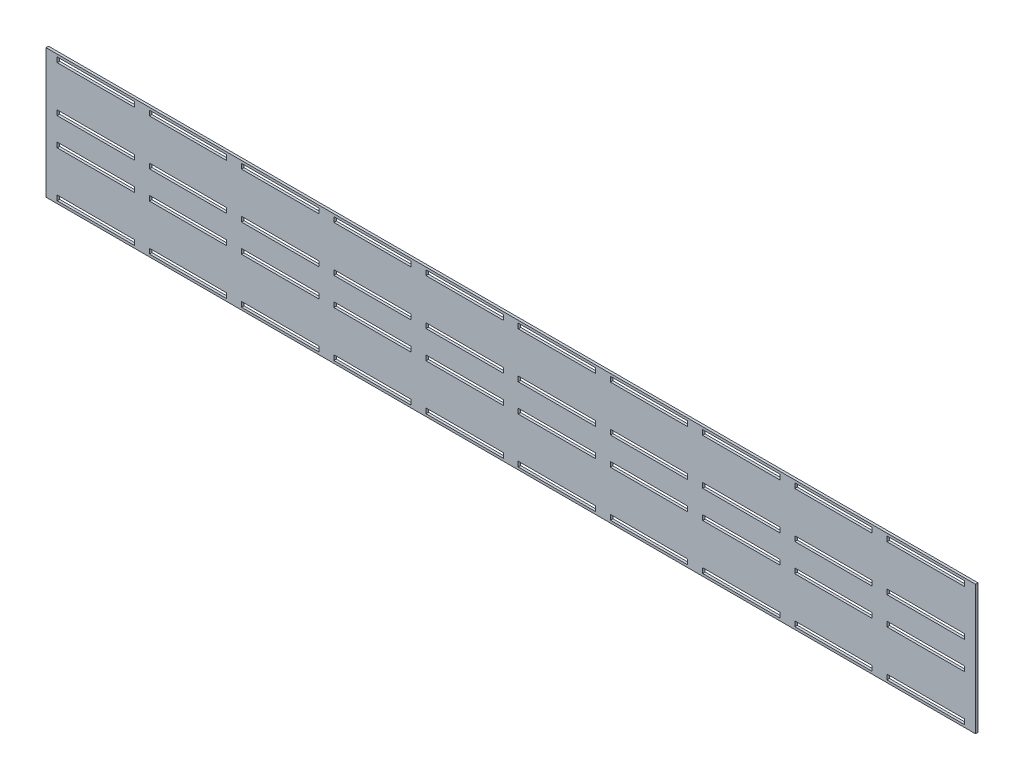
SolidWorks part; units mm, degrees
material "ABS"
ref_plane "Płaszczyzna przednia" through (0, 0, 0) normal (0, 0, 1) x (1, 0, 0)
ref_plane "Płaszczyzna górna" through (0, 0, 0) normal (0, 1, 0) x (1, 0, 0)
ref_plane "Płaszczyzna prawa" through (0, 0, 0) normal (1, 0, 0) x (0, 0, -1)
sketch "Szkic1" plane through (0, 0, 0) normal (0, 0, 1) x (1, 0, 0)
  line L1 (-187, 26.5) -> (187, 26.5)
  line L2 (-187, 26.5) -> (-187, -26.5)
  line L3 (-187, -26.5) -> (187, -26.5)
  line L4 (187, 26.5) -> (187, -26.5)
  line L5 (-187, 26.5) -> (187, -26.5) construction
  line L6 (-187, -26.5) -> (187, 26.5) construction
  point P0 (0, 0)
  dimension "D1" = 374
  dimension "D2" = 53
extrude "Dodanie-wyciągnięcie1" add sketch "Szkic1" along normal blind 1
sketch "Szkic6" plane through (0, 0, 0) normal (0, 0, -1) x (-1, 0, 0)
  line L2 (-182, -6.6) -> (-151, -6.6)
  line L8 (-145, -6.6) -> (-114, -6.6)
  line L13 (-108, -6.6) -> (-77, -6.6)
  line L15 (-182, -6.6) -> (-182, -4.6)
  line L20 (-182, -4.6) -> (-151, -4.6)
  line L23 (-34, -6.6) -> (-3, -6.6)
  line L25 (-151, -4.6) -> (-151, -6.6)
  line L28 (3, -6.6) -> (34, -6.6)
  line L33 (40, -6.6) -> (71, -6.6)
  line L38 (77, -6.6) -> (108, -6.6)
  line L43 (114, -6.6) -> (145, -6.6)
  line L45 (-145, -6.6) -> (-145, -4.6)
  line L48 (151, -6.6) -> (182, -6.6)
  line L50 (-145, -4.6) -> (-114, -4.6)
  line L51 (-114, -4.6) -> (-114, -6.6)
  line L55 (-108, -6.6) -> (-108, -4.6)
  line L56 (-108, -4.6) -> (-77, -4.6)
  line L57 (-77, -4.6) -> (-77, -6.6)
  line L67 (-34, -6.6) -> (-34, -4.6)
  line L68 (-34, -4.6) -> (-3, -4.6)
  line L69 (-3, -4.6) -> (-3, -6.6)
  line L73 (3, -6.6) -> (3, -4.6)
  line L74 (3, -4.6) -> (34, -4.6)
  line L75 (34, -4.6) -> (34, -6.6)
  line L79 (40, -6.6) -> (40, -4.6)
  line L80 (40, -4.6) -> (71, -4.6)
  line L81 (71, -4.6) -> (71, -6.6)
  line L82 (77, -6.6) -> (77, -4.6)
  line L83 (77, -4.6) -> (108, -4.6)
  line L84 (108, -4.6) -> (108, -6.6)
  line L91 (114, -6.6) -> (114, -4.6)
  line L92 (114, -4.6) -> (145, -4.6)
  line L93 (145, -4.6) -> (145, -6.6)
  line L94 (151, -6.6) -> (151, -4.6)
  line L95 (151, -4.6) -> (182, -4.6)
  line L96 (182, -4.6) -> (182, -6.6)
  line L100 (-114, -25) -> (-114, -23)
  line L101 (-187, 26.5) -> (187, 26.5) construction
  line L102 (-187, -26.5) -> (-187, 26.5) construction
  line L103 (-182, 25) -> (-151, 25)
  line L104 (-182, 25) -> (-182, 23)
  line L105 (-182, 23) -> (-151, 23)
  line L106 (-151, 25) -> (-151, 23)
  line L107 (-151, -25) -> (-151, -23)
  line L108 (-182, -23) -> (-151, -23)
  line L109 (-182, -25) -> (-182, -23)
  line L110 (-182, -25) -> (-151, -25)
  line L111 (-145, -23) -> (-114, -23)
  line L112 (-145, -25) -> (-145, -23)
  line L113 (-145, -25) -> (-114, -25)
  line L114 (-145, 25) -> (-114, 25)
  line L115 (-145, 25) -> (-145, 23)
  line L116 (-145, 23) -> (-114, 23)
  line L117 (-114, 25) -> (-114, 23)
  line L118 (-77, -25) -> (-77, -23)
  line L119 (-108, -23) -> (-77, -23)
  line L120 (-108, -25) -> (-108, -23)
  line L121 (-108, -25) -> (-77, -25)
  line L122 (-108, 25) -> (-77, 25)
  line L123 (-108, 25) -> (-108, 23)
  line L124 (-108, 23) -> (-77, 23)
  line L125 (-77, 25) -> (-77, 23)
  line L126 (-40, -25) -> (-40, -23)
  line L127 (-71, -23) -> (-40, -23)
  line L128 (-71, -25) -> (-71, -23)
  line L129 (-71, -25) -> (-40, -25)
  line L130 (-71, 25) -> (-40, 25)
  line L131 (-71, 25) -> (-71, 23)
  line L132 (-71, 23) -> (-40, 23)
  line L133 (-40, 25) -> (-40, 23)
  line L134 (-3, -25) -> (-3, -23)
  line L135 (-34, -23) -> (-3, -23)
  line L136 (-34, -25) -> (-34, -23)
  line L137 (-34, -25) -> (-3, -25)
  line L138 (-34, 25) -> (-3, 25)
  line L139 (-34, 25) -> (-34, 23)
  line L140 (-34, 23) -> (-3, 23)
  line L141 (-3, 25) -> (-3, 23)
  line L142 (34, -25) -> (34, -23)
  line L143 (3, -23) -> (34, -23)
  line L144 (3, -25) -> (3, -23)
  line L145 (3, -25) -> (34, -25)
  line L146 (3, 25) -> (34, 25)
  line L147 (3, 25) -> (3, 23)
  line L148 (3, 23) -> (34, 23)
  line L149 (34, 25) -> (34, 23)
  line L150 (71, -25) -> (71, -23)
  line L151 (40, -23) -> (71, -23)
  line L152 (40, -25) -> (40, -23)
  line L153 (40, -25) -> (71, -25)
  line L154 (40, 25) -> (71, 25)
  line L155 (40, 25) -> (40, 23)
  line L156 (40, 23) -> (71, 23)
  line L157 (71, 25) -> (71, 23)
  line L158 (108, -25) -> (108, -23)
  line L159 (77, -23) -> (108, -23)
  line L160 (77, -25) -> (77, -23)
  line L161 (77, -25) -> (108, -25)
  line L162 (77, 25) -> (108, 25)
  line L163 (77, 25) -> (77, 23)
  line L164 (77, 23) -> (108, 23)
  line L165 (108, 25) -> (108, 23)
  line L166 (145, -25) -> (145, -23)
  line L167 (114, -23) -> (145, -23)
  line L168 (114, -25) -> (114, -23)
  line L169 (114, -25) -> (145, -25)
  line L170 (114, 25) -> (145, 25)
  line L171 (114, 25) -> (114, 23)
  line L172 (114, 23) -> (145, 23)
  line L173 (145, 25) -> (145, 23)
  line L174 (182, -25) -> (182, -23)
  line L175 (151, -23) -> (182, -23)
  line L176 (151, -25) -> (151, -23)
  line L177 (151, -25) -> (182, -25)
  line L178 (151, 25) -> (182, 25)
  line L179 (151, 25) -> (151, 23)
  line L180 (151, 23) -> (182, 23)
  line L181 (182, 25) -> (182, 23)
  line L182 (187, -26.5) -> (-187, -26.5) construction
  line L183 (-145, 4.6) -> (-114, 4.6)
  line L184 (-145, 4.6) -> (-145, 6.6)
  line L185 (-71, -6.6) -> (-40, -6.6)
  line L186 (-71, -6.6) -> (-71, -4.6)
  line L187 (-71, -4.6) -> (-40, -4.6)
  line L188 (-40, -6.6) -> (-40, -4.6)
  line L189 (-182, 4.6) -> (-151, 4.6)
  line L190 (-182, 4.6) -> (-182, 6.6)
  line L191 (-182, 6.6) -> (-151, 6.6)
  line L192 (-151, 4.6) -> (-151, 6.6)
  line L193 (-145, 6.6) -> (-114, 6.6)
  line L194 (-114, 4.6) -> (-114, 6.6)
  line L195 (-108, 4.6) -> (-77, 4.6)
  line L196 (-108, 4.6) -> (-108, 6.6)
  line L197 (-108, 6.6) -> (-77, 6.6)
  line L198 (-77, 4.6) -> (-77, 6.6)
  line L199 (-71, 4.6) -> (-40, 4.6)
  line L200 (-71, 4.6) -> (-71, 6.6)
  line L201 (-71, 6.6) -> (-40, 6.6)
  line L202 (-40, 4.6) -> (-40, 6.6)
  line L203 (-34, 4.6) -> (-3, 4.6)
  line L204 (-34, 4.6) -> (-34, 6.6)
  line L205 (-34, 6.6) -> (-3, 6.6)
  line L206 (-3, 4.6) -> (-3, 6.6)
  line L207 (3, 4.6) -> (34, 4.6)
  line L208 (3, 4.6) -> (3, 6.6)
  line L209 (3, 6.6) -> (34, 6.6)
  line L210 (34, 4.6) -> (34, 6.6)
  line L211 (40, 4.6) -> (71, 4.6)
  line L212 (40, 4.6) -> (40, 6.6)
  line L213 (40, 6.6) -> (71, 6.6)
  line L214 (71, 4.6) -> (71, 6.6)
  line L215 (77, 4.6) -> (108, 4.6)
  line L216 (77, 4.6) -> (77, 6.6)
  line L217 (77, 6.6) -> (108, 6.6)
  line L218 (108, 4.6) -> (108, 6.6)
  line L219 (114, 4.6) -> (145, 4.6)
  line L220 (114, 4.6) -> (114, 6.6)
  line L221 (114, 6.6) -> (145, 6.6)
  line L222 (145, 4.6) -> (145, 6.6)
  line L223 (151, 4.6) -> (182, 4.6)
  line L224 (151, 4.6) -> (151, 6.6)
  line L225 (151, 6.6) -> (182, 6.6)
  line L226 (182, 4.6) -> (182, 6.6)
  dimension "D1" = 10
  dimension "D3" = 31
  dimension "D21" = 10
  dimension "D22" = 6
  dimension "D23" = 1.5
  dimension "D24" = 5
  dimension "D25" = 1.5
  dimension "D26" = 5
extrude "Wytnij-wyciągnięcie1" cut sketch "Szkic6" against normal blind 2
sketch "Szkic7" plane through (0, 0, 0) normal (0, 0, -1) x (-1, 0, 0)
  line L2 (-187, 26.5) -> (187, 26.5)
  line L4 (-187, 26.5) -> (-187, -26.5)
  line L6 (-187, -26.5) -> (187, -26.5)
  line L8 (187, 26.5) -> (187, -26.5)
  line L9 (186.5, -26) -> (-186.5, -26)
  line L10 (186.5, -26) -> (186.5, 26)
  line L11 (186.5, 26) -> (-186.5, 26)
  line L12 (-186.5, -26) -> (-186.5, 26)
extrude "Wytnij-wyciągnięcie2" cut sketch "Szkic7" against normal blind 10
